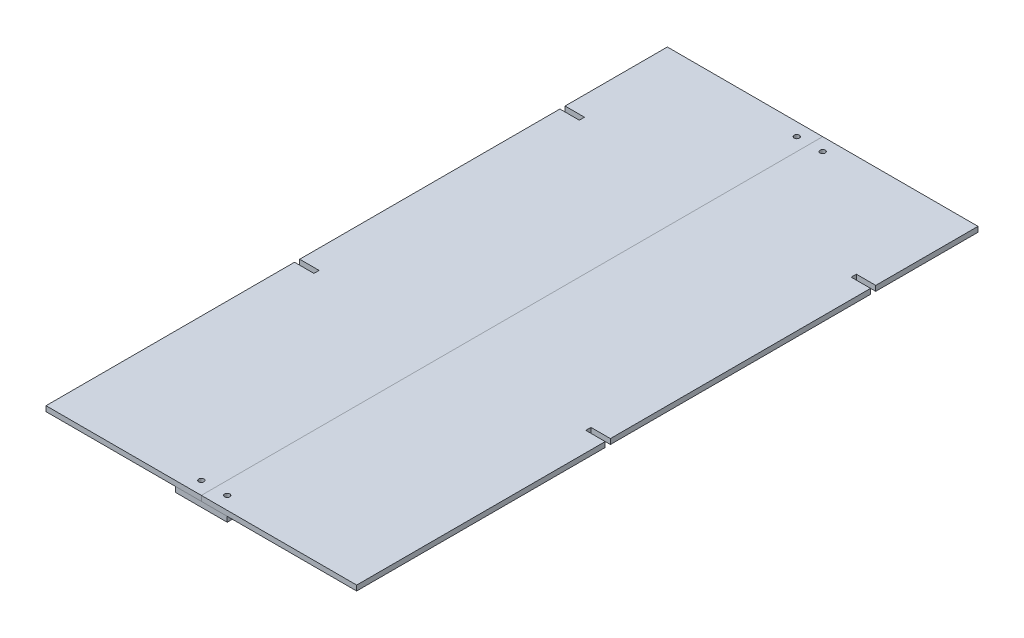
SolidWorks part; units mm, degrees
material "Cedar"
ref_plane "Front Plane" through (0, 0, 0) normal (0, 0, 1) x (1, 0, 0)
ref_plane "Top Plane" through (0, 0, 0) normal (0, 1, 0) x (1, 0, 0)
ref_plane "Right Plane" through (0, 0, 0) normal (1, 0, 0) x (0, 0, -1)
sketch "Sketch1" plane through (0, 0, 0) normal (0, 1, 0) x (1, 0, 0)
  line L0 (0, -2.794) -> (0, 2.794) construction
  line L1 (152.4, -304.8) -> (-152.4, -304.8)
  line L2 (152.4, -304.8) -> (152.4, 304.8)
  line L3 (152.4, 304.8) -> (-152.4, 304.8)
  line L4 (-152.4, -304.8) -> (-152.4, 304.8)
  line L5 (-2.794, 0) -> (2.794, 0) construction
  point P6 (0, -304.8)
  point P7 (-152.4, 0)
  dimension "D1" = 609.6
  dimension "D2" = 304.8
extrude "Boss-Extrude1" add sketch "Sketch1" along normal blind 5.08
sketch "Sketch2" plane through (0, 5.08, 0) normal (0, 1, 0) x (1, 0, 0)
  line L0 (152.4, -304.8) -> (152.4, 304.8) construction
  line L1 (152.4, -60.96) -> (133.35, -60.96)
  line L2 (152.4, -60.96) -> (152.4, -55.88)
  line L3 (152.4, -55.88) -> (133.35, -55.88)
  line L4 (133.35, -60.96) -> (133.35, -55.88)
  line L5 (-152.4, -304.8) -> (152.4, -304.8) construction
  line L6 (152.4, 204.47) -> (133.35, 204.47)
  line L7 (152.4, 204.47) -> (152.4, 199.39)
  line L8 (152.4, 199.39) -> (133.35, 199.39)
  line L9 (133.35, 204.47) -> (133.35, 199.39)
  line L10 (0, -304.8) -> (0, 304.8) construction
  line L11 (152.4, 304.8) -> (-152.4, 304.8) construction
  line L12 (-133.35, 204.47) -> (-133.35, 199.39)
  line L13 (-152.4, 199.39) -> (-133.35, 199.39)
  line L14 (-152.4, 204.47) -> (-152.4, 199.39)
  line L15 (-152.4, 204.47) -> (-133.35, 204.47)
  line L16 (-133.35, -60.96) -> (-133.35, -55.88)
  line L17 (-152.4, -55.88) -> (-133.35, -55.88)
  line L18 (-152.4, -60.96) -> (-152.4, -55.88)
  line L19 (-152.4, -60.96) -> (-133.35, -60.96)
  dimension "D1" = 243.84
  dimension "D2" = 504.19
  dimension "D3" = 5.08
  dimension "D4" = 19.05
extrude "Cut-Extrude1" cut sketch "Sketch2" against normal through all
split "Split1" trim tools "Right Plane" bodies to split 102 resulting bodies 103 104
hole_wizard "#10 Clearance Hole1" positions "Sketch5" profile "Sketch6" hole size "#10" standard "ANSI Inch" end condition through all
sketch "Sketch5" plane through (0, 5.08, 0) normal (0, 1, 0) x (1, 0, 0)
  line L1 (12.7, -292.1) -> (-12.7, -292.1)
  line L2 (12.7, -292.1) -> (12.7, 292.1)
  line L3 (12.7, 292.1) -> (-12.7, 292.1)
  line L4 (-12.7, -292.1) -> (-12.7, 292.1)
  line L5 (12.7, -292.1) -> (-12.7, 292.1) construction
  line L6 (12.7, 292.1) -> (-12.7, -292.1) construction
  line L7 (0, 304.8) -> (-152.4, 304.8) construction
  point P2 (-12.7, 292.1)
  point P121 (12.7, -292.1)
  point P122 (12.7, 292.1)
  point P123 (-12.7, -292.1)
  point P127 (0, 0)
  dimension "D1" = 25.4
  dimension "D2" = 12.7
sketch "Sketch6" plane through (-12.7, 5.08, -292.1) normal (1, 0, 0) x (0, 0, 1)
  line L0 (0, 0) -> (0, 5.08)
  line L1 (0, 5.08) -> (2.5527, 5.08)
  line L2 (2.5527, 5.08) -> (2.5527, 0)
  line L5 (2.5527, 0) -> (0, 0)
  line L11 (0, -6.35) -> (0, 107.95) construction
  dimension "Thru Hole Dia." = 5.1054
  dimension "Thru Hole Depth" = 5.08
sketch "Sketch7" plane through (0, 0, 0) normal (0, -1, 0) x (1, 0, 0)
  line L0 (0, -304.8) -> (-152.4, -304.8) construction
  line L1 (25.4, 304.8) -> (-25.4, 304.8)
  line L2 (25.4, 304.8) -> (25.4, -304.8)
  line L3 (25.4, -304.8) -> (-25.4, -304.8)
  line L4 (-25.4, 304.8) -> (-25.4, -304.8)
  line L5 (25.4, 304.8) -> (-25.4, -304.8) construction
  line L6 (25.4, -304.8) -> (-25.4, 304.8) construction
  circle A0 centre (12.7, -292.1) radius 2.5527 construction
  point P0 (0, 0)
  dimension "D1" = 12.7
extrude "Boss-Extrude2" add sketch "Sketch7" along normal blind 5.08 separate body
hole_wizard "#10-32 Tapped Hole1" positions "Sketch8" profile "Sketch9" tap size "#10-32" standard "ANSI Inch" end condition through all
sketch "Sketch8" plane through (0, 0, 0) normal (0, 1, 0) x (1, 0, 0)
  point P0 (-12.7, -292.1)
  point P3 (12.7, -292.1)
  point P6 (-12.7, 292.1)
  point P9 (12.7, 292.1)
sketch "Sketch9" plane through (-12.7, 0, 292.1) normal (1, 0, 0) x (0, 0, 1)
  line L0 (0, 0) -> (0, 5.08)
  line L1 (0, 5.08) -> (2.0193, 5.08)
  line L2 (2.0193, 5.08) -> (2.0193, 0)
  line L5 (2.0193, 0) -> (0, 0)
  line L11 (0, -6.35) -> (0, 107.95) construction
  dimension "Thru Tap Drill Dia." = 4.0386
  dimension "Thru Tap Drill Depth" = 5.08
cosmetic thread "Hole Thread1" parameters "D2"=4.826
cosmetic thread "Hole Thread2" parameters "D2"=4.826
cosmetic thread "Hole Thread3" parameters "D2"=4.826
cosmetic thread "Hole Thread4" parameters "D2"=4.826
